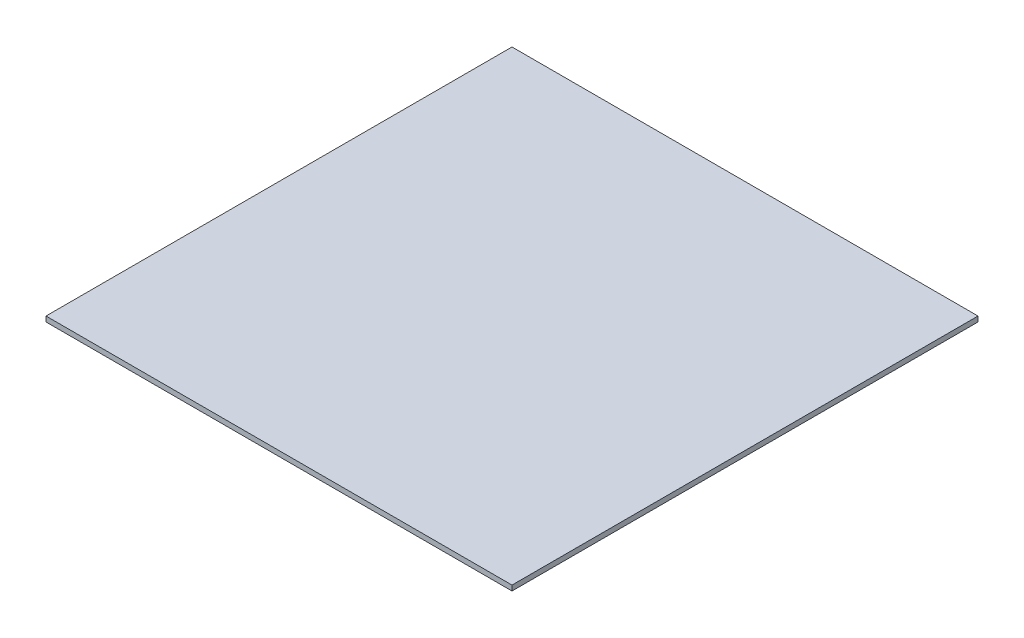
SolidWorks part; units mm, degrees
ref_plane "前视基准面" through (0, 0, 0) normal (0, 0, 1) x (1, 0, 0)
ref_plane "上视基准面" through (0, 0, 0) normal (0, 1, 0) x (1, 0, 0)
ref_plane "右视基准面" through (0, 0, 0) normal (1, 0, 0) x (0, 0, -1)
sketch "草图1" plane through (0, 0, 0) normal (0, 1, 0) x (1, 0, 0)
  line L1 (-135, 135) -> (135, 135)
  line L2 (-135, 135) -> (-135, -135)
  line L3 (-135, -135) -> (135, -135)
  line L4 (135, 135) -> (135, -135)
  line L5 (-135, 135) -> (135, -135) construction
  line L6 (-135, -135) -> (135, 135) construction
  point P0 (0, 0)
  dimension "D1" = 270
  dimension "D2" = 270
extrude "凸台-拉伸1" add sketch "草图1" along normal blind 3
